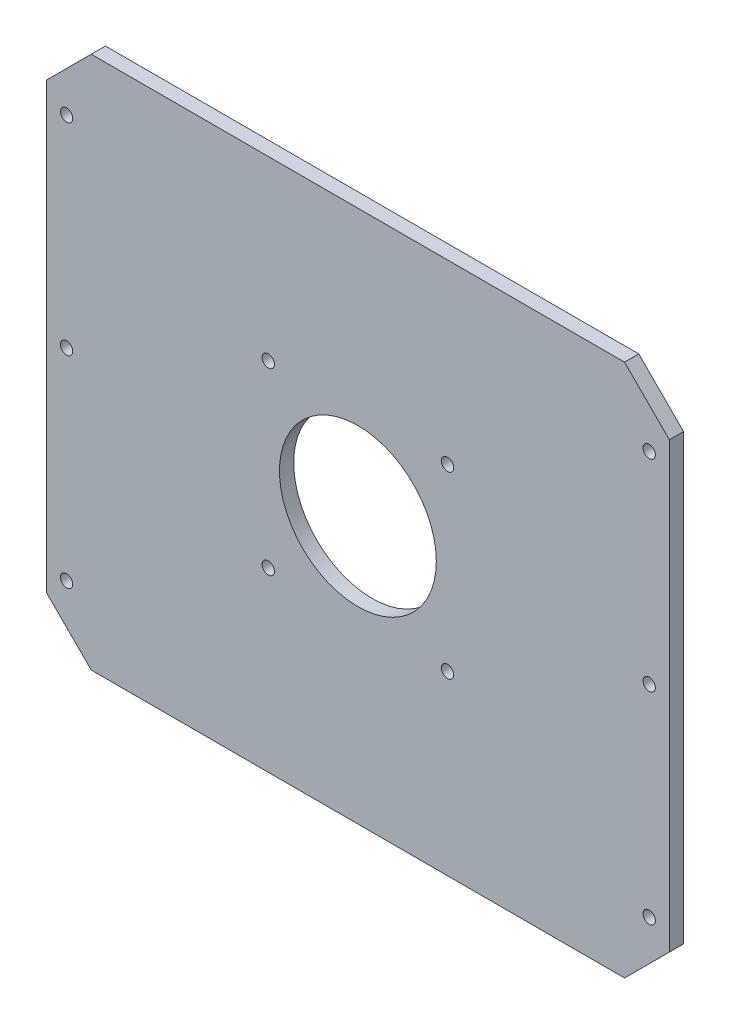
SolidWorks part; units mm, degrees
ref_plane "Front Plane" through (0, 0, 0) normal (0, 0, 1) x (1, 0, 0)
ref_plane "Top Plane" through (0, 0, 0) normal (0, 1, 0) x (1, 0, 0)
ref_plane "Right Plane" through (0, 0, 0) normal (1, 0, 0) x (0, 0, -1)
sketch "Sketch1" plane through (0, 0, 0) normal (0, 0, 1) x (1, 0, 0)
  line L0 (-79.0045, 0) -> (94.053, 0) construction
  line L1 (0, 67.0127) -> (0, -68.6587) construction
  line L3 (139, -119) -> (-139, -119)
  line L4 (139, -119) -> (139, 119)
  line L5 (139, 119) -> (-139, 119)
  line L6 (-139, -119) -> (-139, 119)
  line L7 (139, -119) -> (-139, 119) construction
  line L8 (139, 119) -> (-139, -119) construction
  point P4 (0, 0)
  dimension "D1" = 238
  dimension "D2" = 278
extrude "Boss-Extrude1" add sketch "Sketch1" along normal blind 6.35
sketch "Sketch2" plane through (0, 0, 6.35) normal (0, 0, 1) x (1, 0, 0)
  line L0 (-156.6091, 0) -> (177.3719, 0) construction
  line L1 (0, 110.6274) -> (0, -105.2428) construction
  circle A0 centre (0, 0) radius 35
  circle A1 centre (-40, 40) radius 2.75
  circle A2 centre (40, 40) radius 2.75
  circle A3 centre (40, -40) radius 2.75
  circle A4 centre (-40, -40) radius 2.75
  dimension "D1" = 40
  dimension "D2" = 5.5
  dimension "D3" = 70
  dimension "D4" = 40
extrude "Cut-Extrude1" cut sketch "Sketch2" against normal through all
chamfer "Chamfer1" distance 20 angle 45 4 edges at (139, -119, 3.175) (139, 119, 3.175) (-139, 119, 3.175) (-139, -119, 3.175)
sketch "Sketch4" plane through (0, 0, 6.35) normal (0, 0, 1) x (1, 0, 0)
  line L1 (219.7737, 0) -> (-232.7917, 0) construction
  line L4 (-139, 99) -> (-139, -99) construction
  circle A6 centre (-130, 90) radius 2.75
  circle A7 centre (130, 90) radius 2.75
  circle A8 centre (-130, -90) radius 2.75
  circle A9 centre (130, -90) radius 2.75
  circle A10 centre (-130, 0) radius 2.75
  circle A11 centre (130, 0) radius 2.75
  dimension "D4" = 5.5
  dimension "D7" = 5.5
  dimension "D5" = 9
  dimension "D6" = 90
extrude "Cut-Extrude2" cut sketch "Sketch4" against normal blind 76.2
equation "\"plate_thickness\"= 6.35 'thickness of the plate "
equation "\"height\"= 180"
equation "\"D1@Boss-Extrude1\"=\"plate_thickness\""
equation "\"t_height\"= 200"
equation "\"t_width\"= 240"
equation "\"t_length\"= 240"
equation "\"plate_spacing\"= 1"
equation "\"front_plate_height\"= \"t_height\" + 38"
equation "\"front_plate_width\"= \"t_width\" + 38"
equation "\"side_plate_height\"= \"front_plate_height\""
equation "\"side_plate_length\"= \"t_length\" + 38"
equation "\"top_plate_width\"= \"front_plate_width\""
equation "\"top_plate_length\"= \"side_plate_length\""
equation "\"D2@Sketch1\"=\"front_plate_width\""
equation "\"D1@Sketch1\"=\"front_plate_height\""
equation "\"plate_hole_spacing\"= 9"
equation "\"connector_D1\"= 70 'the big holes diameter"
equation "\"connector_mtg_D2\"= 5.5 'mounting holes"
equation "\"mtg_dfc\"= 40 'mounting hole distance from center"
equation "\"D3@Sketch2\"=\"connector_D1\""
equation "\"D2@Sketch2\"=\"mtg_hole_D\""
equation "\"D4@Sketch2\"=\"mtg_dfc\""
equation "\"D1@Sketch2\"=\"mtg_dfc\""
equation "\"mtg_hole_D\"= 5.5 'mounting holes"
equation "\"plate_hole_from_edge\"= 9"
equation "\"itx_support_t_slot_length\"= \"t_width\" + (2 * 20.5)"
equation "\"locomotion_length\"= \"t_length\""
equation "\"locomotion_width\"= \"t_width\""
equation "\"locomotion_height\"= 40"
equation "\"itx_mtg_hole_spacing\"= 40"
equation "\"emg30_bracket_hole_len\"= 60"
equation "\"emg30_bracket_hole_wid\"= 11"
equation "\"D4@Sketch4\"=\"mtg_hole_D\""
equation "\"D5@Sketch4\"=\"plate_hole_spacing\""
equation "\"D6@Sketch4\"=90"
equation "\"D7@Sketch4\"=\"mtg_hole_D\""
